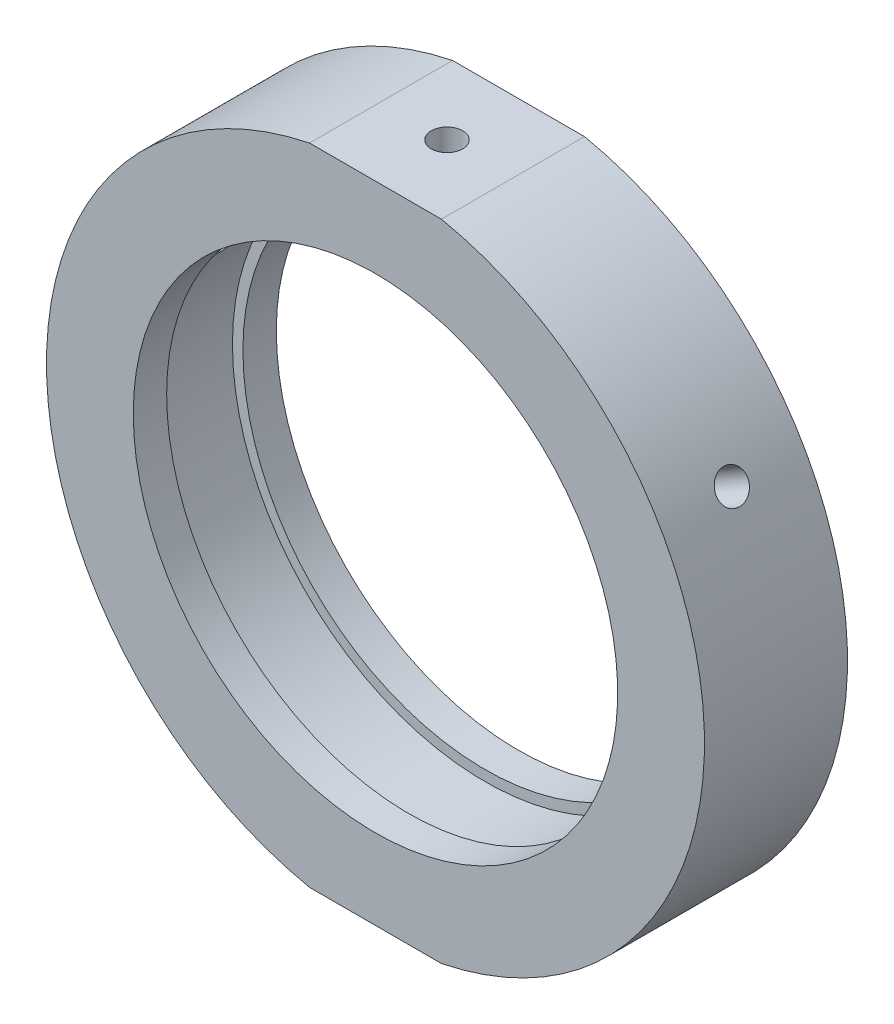
SolidWorks part; units mm, degrees
ref_plane "前视基准面" through (0, 0, 0) normal (0, 0, 1) x (1, 0, 0)
ref_plane "上视基准面" through (0, 0, 0) normal (0, 1, 0) x (1, 0, 0)
ref_plane "右视基准面" through (0, 0, 0) normal (1, 0, 0) x (0, 0, -1)
sketch "草图1" plane through (0, 0, 0) normal (0, 1, 0) x (1, 0, 0)
  line L0 (0, 31.9391) -> (0, -26.491) construction
  line L1 (34.5, 7.5) -> (34.5, -7.5)
  line L6 (34.5, -7.5) -> (25.4, -7.5)
  line L7 (25.4, -7.5) -> (25.4, -4)
  line L8 (25.4, -4) -> (26.5, -4)
  line L9 (26.5, -4) -> (26.5, 4)
  line L10 (26.5, 4) -> (25.4, 4)
  line L11 (25.4, 4) -> (25.4, 7.5)
  line L12 (25.4, 7.5) -> (34.5, 7.5)
  line L17 (19.05, 0) -> (-5.0345, 0) construction
  point P6 (26.5, 0)
  dimension "D2" = 26.5
  dimension "D3" = 25.4
  dimension "D4" = 25.4
  dimension "D5" = 15
  dimension "D6" = 3.5
  dimension "D9" = 34.5
  dimension "D14" = 8
  dimension "D15" = 4
  dimension "D18" = 0
revolve "旋转1" add sketch "草图1" angle 360 about L0
sketch "草图2" plane through (0, 0, 7.5) normal (0, 0, 1) x (1, 0, 0)
  line L0 (0, 0) -> (43.1523, 0) construction
  line L1 (-33.152, 43.0489) -> (30.8698, 43.0489)
  line L2 (-33.152, 43.0489) -> (-33.152, 33.8)
  line L3 (-33.152, 33.8) -> (30.8698, 33.8)
  line L4 (30.8698, 43.0489) -> (30.8698, 33.8)
  line L5 (30.8698, -43.0489) -> (30.8698, -33.8)
  line L6 (-33.152, -33.8) -> (30.8698, -33.8)
  line L7 (-33.152, -43.0489) -> (-33.152, -33.8)
  line L8 (-33.152, -43.0489) -> (30.8698, -43.0489)
  dimension "D1" = 33.8
extrude "切除-拉伸1" cut sketch "草图2" against normal blind 49
sketch "草图10" plane through (0, 0, 0) normal (0, 0, 1) x (1, 0, 0)
  line L0 (0, 33.8) -> (0, -33.8)
  line L1 (-6.9145, 33.8) -> (6.9145, 33.8) construction
  line L2 (-6.9145, -33.8) -> (6.9145, -33.8) construction
  line L3 (0, 0) -> (-29.8779, 17.25)
  line L4 (0, 0) -> (29.8779, 17.25)
  arc A2 (6.9145, -33.8) -> (6.9145, 33.8) centre (0, 0) ccw construction
  arc A3 (-6.9145, 33.8) -> (-6.9145, -33.8) centre (0, 0) ccw construction
  arc A4 (29.8779, 17.25) -> (6.9145, 33.8) centre (0, 0) ccw
  arc A5 (-6.9145, 33.8) -> (-29.8779, 17.25) centre (0, 0) ccw
  dimension "D1" = 60
  dimension "D2" = 60
hole_wizard "M4 螺纹孔2" positions "草图15" profile "草图16" tap size "M4" standard "ISO"
sketch "草图15" plane through (0, 33.8, 0) normal (0, 1, 0) x (1, 0, 0)
  point P0 (0, 0)
  point P3 (0, 0)
  point P4 (0, 0)
sketch "草图16" plane through (0, 33.8, 0) normal (1, 0, 0) x (0, 0, 1)
  line L0 (0, 0) -> (0, 6.4914)
  line L1 (0, 6.4914) -> (1.65, 5.5)
  line L2 (1.65, 5.5) -> (1.65, 0)
  line L5 (1.65, 0) -> (0, 0)
  line L10 (0, 6.4914) -> (-1.65, 5.5) construction
  line L11 (0, -6.35) -> (0, 107.95) construction
  dimension "螺纹孔钻头直径" = 3.3
  dimension "螺纹孔钻头深度" = 5.5
  dimension "导头角度" = 118
cosmetic thread "孔螺蚊线1" parameters "D1"=5.5, "D2"=4
hole_wizard "M6 螺纹孔2" positions "草图17" profile "草图18" tap size "M6" standard "ISO"
sketch "草图17" plane through (0, -33.8, 0) normal (0, -1, 0) x (-1, 0, 0)
  point P0 (0, 0)
  point P3 (0, 0)
sketch "草图18" plane through (0, -33.8, 0) normal (1, 0, 0) x (0, 0, -1)
  line L0 (0, 0) -> (0, 7.0022)
  line L1 (0, 7.0022) -> (2.5, 5.5)
  line L2 (2.5, 5.5) -> (2.5, 0)
  line L5 (2.5, 0) -> (0, 0)
  line L10 (0, 7.0022) -> (-2.5, 5.5) construction
  line L11 (0, -6.35) -> (0, 107.95) construction
  dimension "螺纹孔钻头直径" = 5
  dimension "螺纹孔钻头深度" = 5.5
  dimension "导头角度" = 118
cosmetic thread "孔螺蚊线2" parameters "D1"=5.5, "D2"=6
hole_wizard "M4 螺纹孔3" positions "3D草图4" profile "草图22" tap size "M4" standard "ISO"
sketch3d "3D草图4"
  point P0 (-29.8779, 17.25, 0)
  point P4 (29.8779, 17.25, 0)
  point P7 (29.8779, 17.25, 0)
  point P11 (-29.8779, 17.25, 0)
  point P15 (29.8779, 17.25, 0)
  point P17 (29.8779, 17.25, 0)
  point P20 (29.8779, 17.25, 0)
sketch "草图22" plane through (29.8779, 17.25, 0) normal (0, 0, 1) x (-0.5, 0.866, 0)
  line L0 (0, 0) -> (0, 14.3914)
  line L1 (0, 14.3914) -> (1.65, 13.4)
  line L2 (1.65, 13.4) -> (1.65, 0)
  line L5 (1.65, 0) -> (0, 0)
  line L10 (0, 14.3914) -> (-1.65, 13.4) construction
  line L11 (0, -6.35) -> (0, 107.95) construction
  dimension "螺纹孔钻头直径" = 3.3
  dimension "螺纹孔钻头深度" = 13.4
  dimension "导头角度" = 118
cosmetic thread "孔螺蚊线4" parameters "D1"=8.0514, "D2"=4
cosmetic thread "孔螺蚊线5" parameters "D1"=8.0514, "D2"=4
